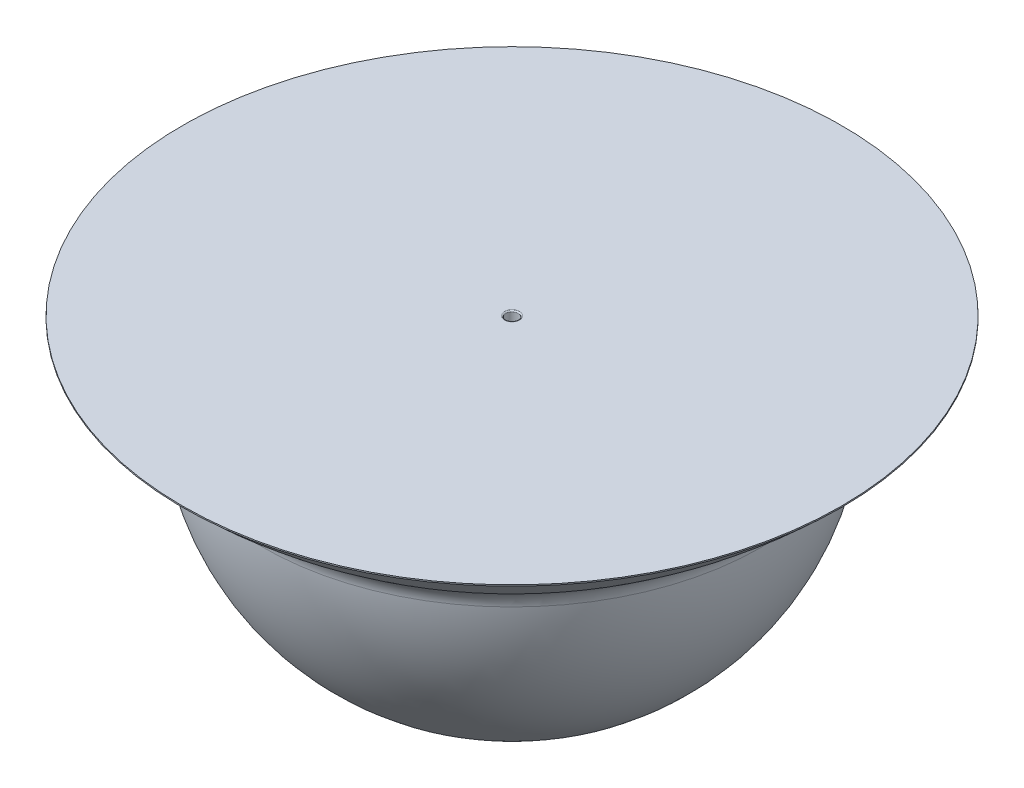
SolidWorks part; units mm, degrees
material "ABS"
ref_plane "Front Plane" through (0, 0, 0) normal (0, 0, 1) x (1, 0, 0)
ref_plane "Top Plane" through (0, 0, 0) normal (0, 1, 0) x (1, 0, 0)
ref_plane "Right Plane" through (0, 0, 0) normal (1, 0, 0) x (0, 0, -1)
sketch "Sketch2" plane through (0, 0, 0) normal (0, 0, 1) x (1, 0, 0)
  line L0 (0, 50) -> (0, -200)
  line L1 (0, 50) -> (264.4272, 50)
  arc A0 (0, -200) -> (200, 0) centre (0, 0) ccw
  arc A1 (200, 0) -> (264.4272, 50) centre (0, 324.2173) ccw
revolve "Revolve1" add sketch "Sketch2" angle 360 about L0
fillet "Fillet1" radius 20 1 edges at (0, 0, 200)
shell "Shell1" thickness 1
ref_plane "Plane1" through (0, 50, 0) normal (0, 1, 0) x (1, 0, 0)
sketch "Sketch3" plane through (0, 50, 0) normal (0, 1, 0) x (1, 0, 0)
  circle A0 centre (0, 0) radius 264.4272
extrude "Boss-Extrude1" add sketch "Sketch3" along normal blind 1
sketch "Sketch4" plane through (0, 51, 0) normal (0, 1, 0) x (1, 0, 0)
  circle A0 centre (0, 0) radius 5
extrude "Cut-Extrude1" cut sketch "Sketch4" against normal through all
sketch "Sketch6" plane through (0, 51, 0) normal (0, 1, 0) x (1, 0, 0)
  circle A0 centre (0, 0) radius 5
  circle A1 centre (0, 0) radius 6
extrude "Boss-Extrude2" add sketch "Sketch6" against normal blind 270
cosmetic thread "Cosmetic Thread1" parameters "D1"=19, "D2"=10.106
fillet "Fillet2" radius 1 1 edges at (0, 51, 5)
